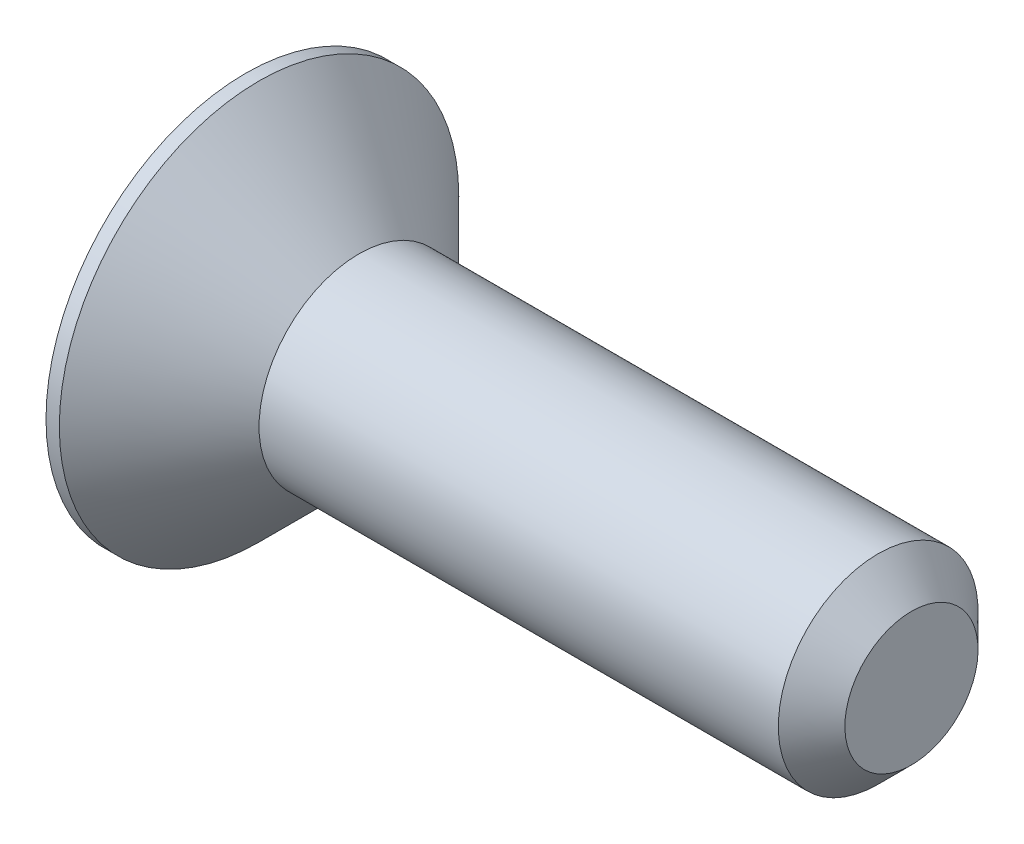
SolidWorks part; units mm, degrees
ref_plane "Plan de face" through (0, 0, 0) normal (0, 0, 1) x (1, 0, 0)
ref_plane "Plan de dessus" through (0, 0, 0) normal (0, 1, 0) x (1, 0, 0)
ref_plane "Plan de droite" through (0, 0, 0) normal (1, 0, 0) x (0, 0, -1)
sketch "Esquisse1" plane through (0, 0, 0) normal (0, 0, 1) x (1, 0, 0)
  line L0 (0, 0) -> (0, 3)
  line L1 (0, 3) -> (0.2, 3)
  line L2 (0.2, 3) -> (1.7, 1.5)
  line L3 (1.7, 1.5) -> (10, 1.5)
  line L4 (10, 1.5) -> (10, 0)
  line L5 (10, 0) -> (0, 0) construction
  line L6 (0, 0) -> (10, 0)
  dimension "D1" = 1.7
  dimension "D2" = 10
  dimension "D3" = 3
  dimension "D4" = 6
  dimension "D5" = 45
revolve "Révolution1" add sketch "Esquisse1" angle 360 about L5
chamfer "Chanfrein1" distance 0.5 angle 45 1 edges at (10, 1.5, 0)
sketch "Esquisse2" plane through (0, 0, 0) normal (-1, 0, 0) x (0, 0, 1)
  line L1 (0, 1.1547) -> (-1, 0.5774)
  line L2 (-1, 0.5774) -> (-1, -0.5774)
  line L3 (-1, -0.5774) -> (0, -1.1547)
  line L4 (0, -1.1547) -> (1, -0.5774)
  line L5 (1, -0.5774) -> (1, 0.5774)
  line L6 (1, 0.5774) -> (0, 1.1547)
  circle A0 centre (0, 0) radius 1 construction
  dimension "D1" = 2
extrude "Enlèv. mat.-Extru.1" cut sketch "Esquisse2" against normal blind 1.2
